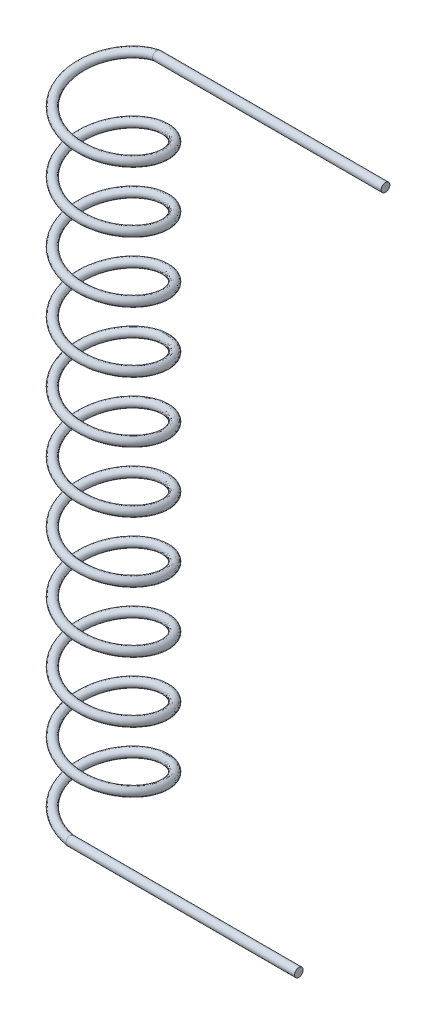
SolidWorks part; units mm, degrees
ref_plane "Front Plane" through (0, 0, 0) normal (0, 0, 1) x (1, 0, 0)
ref_plane "Top Plane" through (0, 0, 0) normal (0, 1, 0) x (1, 0, 0)
ref_plane "Right Plane" through (0, 0, 0) normal (1, 0, 0) x (0, 0, -1)
sketch "Sketch4" plane through (0, 0, 0) normal (0, 1, 0) x (1, 0, 0)
  circle A0 centre (0, 0) radius 25
  dimension "D1" = 50
curve "Helix/Spiral1" pitch 35 height 367.5 turns 10.5
sketch "Sketch5" plane through (0, 0, 0) normal (1, 0, 0) x (0, 0, -1)
  circle A0 centre (-25, 0) radius 2.5
  spline S0 degree 3 poles (-25, 0) (-25, 0.5196) (-24.3389, 1.5646) (-21.4416, 3.1275) (-16.8654, 4.6915) (-10.9687, 6.2553) (-4.2132, 7.8192) (2.8722, 9.383) (9.7327, 10.9468) (15.8311, 12.5106) (20.6901, 14.0745) (23.929, 15.6383) (25.2943, 17.2021) (24.6792, 18.766) (22.1318, 20.3298) (17.8514, 21.8936) (12.1734, 23.4574) (5.5422, 25.0213) (-1.5229, 26.5851) (-8.4688, 28.1489) (-14.7516, 29.7128) (-19.8794, 31.2766) (-23.4507, 32.8404) (-25.1858, 34.4043) (-24.949, 35.9681) (-22.7587, 37.5319) (-18.7865, 39.0957) (-13.3433, 40.6596) (-6.8554, 42.2234) (0.1693, 43.7872) (7.1807, 45.3511) (13.6299, 46.9149) (19.0119, 48.4787) (22.9053, 50.0426) (25.0053, 51.6064) (25.1474, 53.1702) (23.3206, 54.734) (19.6678, 56.2979) (14.475, 57.8617) (8.1489, 59.4255) (1.1848, 60.9894) (-5.8721, 62.5532) (-12.4693, 64.117) (-18.0901, 65.6809) (-22.2945, 67.2447) (-24.7533, 68.8085) (-25.274, 70.3723) (-23.8158, 71.9362) (-20.4928, 73.5) (-15.5654, 75.0638) (-9.4192, 76.6277) (-2.5355, 78.1915) (4.5467, 79.7553) (11.273, 81.3191) (17.1165, 82.883) (21.6199, 84.4468) (24.4305, 86.0106) (25.3283, 87.5745) (24.2429, 89.1383) (21.2593, 90.7021) (16.6112, 92.266) (10.6625, 93.8298) (3.8789, 95.3936) (-3.2084, 96.9574) (-10.0444, 98.5213) (-16.0941, 100.0851) (-20.8836, 101.6489) (-24.0379, 103.2128) (-25.3102, 104.7766) (-24.6007, 106.3404) (-21.9651, 107.9043) (-17.6096, 109.4681) (-11.8754, 111.0319) (-5.2113, 112.5957) (1.8608, 114.1596) (8.7872, 115.7234) (15.0256, 117.2872) (20.0875, 118.8511) (23.5766, 120.4149) (25.2197, 121.9787) (24.8882, 123.5426) (22.608, 125.1064) (18.5576, 126.6702) (13.0543, 128.234) (6.5288, 129.7979) (-0.5079, 131.3617) (-7.5048, 132.9255) (-13.9141, 134.4894) (-19.234, 136.0532) (-23.0479, 137.617) (-25.0572, 139.1809) (-25.1045, 140.7447) (-23.1863, 142.3085) (-19.4526, 143.8723) (-14.1958, 145.4362) (-7.8276, 147) (-0.8464, 148.5638) (6.201, 150.1277) (12.7629, 151.6915) (18.3255, 153.2553) (22.4533, 154.8191) (24.823, 156.383) (25.2491, 157.9468) (23.6983, 159.5106) (20.292, 161.0745) (15.2968, 162.6383) (9.104, 164.2021) (2.1983, 165.766) (-4.8795, 167.3298) (-11.5752, 168.8936) (-17.3646, 170.4574) (-21.7944, 172.0213) (-24.5178, 173.5851) (-25.3215, 175.1489) (-24.1426, 176.7128) (-21.0733, 178.2766) (-16.3541, 179.8404) (-10.3544, 181.4043) (-3.544, 182.9681) (3.544, 184.5319) (10.3544, 186.0957) (16.3541, 187.6596) (21.0733, 189.2234) (24.1426, 190.7872) (25.3215, 192.3511) (24.5178, 193.9149) (21.7944, 195.4787) (17.3646, 197.0426) (11.5752, 198.6064) (4.8795, 200.1702) (-2.1983, 201.734) (-9.104, 203.2979) (-15.2968, 204.8617) (-20.292, 206.4255) (-23.6983, 207.9894) (-25.2491, 209.5532) (-24.823, 211.117) (-22.4533, 212.6809) (-18.3255, 214.2447) (-12.7629, 215.8085) (-6.201, 217.3723) (0.8464, 218.9362) (7.8276, 220.5) (14.1958, 222.0638) (19.4526, 223.6277) (23.1863, 225.1915) (25.1045, 226.7553) (25.0572, 228.3191) (23.0479, 229.883) (19.234, 231.4468) (13.9141, 233.0106) (7.5048, 234.5745) (0.5079, 236.1383) (-6.5288, 237.7021) (-13.0543, 239.266) (-18.5576, 240.8298) (-22.608, 242.3936) (-24.8882, 243.9574) (-25.2197, 245.5213) (-23.5766, 247.0851) (-20.0875, 248.6489) (-15.0256, 250.2128) (-8.7872, 251.7766) (-1.8608, 253.3404) (5.2113, 254.9043) (11.8754, 256.4681) (17.6096, 258.0319) (21.9651, 259.5957) (24.6007, 261.1596) (25.3102, 262.7234) (24.0379, 264.2872) (20.8836, 265.8511) (16.0941, 267.4149) (10.0444, 268.9787) (3.2084, 270.5426) (-3.8789, 272.1064) (-10.6625, 273.6702) (-16.6112, 275.234) (-21.2593, 276.7979) (-24.2429, 278.3617) (-25.3283, 279.9255) (-24.4305, 281.4894) (-21.6199, 283.0532) (-17.1165, 284.617) (-11.273, 286.1809) (-4.5467, 287.7447) (2.5355, 289.3085) (9.4192, 290.8723) (15.5654, 292.4362) (20.4928, 294) (23.8158, 295.5638) (25.274, 297.1277) (24.7533, 298.6915) (22.2945, 300.2553) (18.0901, 301.8191) (12.4693, 303.383) (5.8721, 304.9468) (-1.1848, 306.5106) (-8.1489, 308.0745) (-14.475, 309.6383) (-19.6678, 311.2021) (-23.3206, 312.766) (-25.1474, 314.3298) (-25.0053, 315.8936) (-22.9053, 317.4574) (-19.0119, 319.0213) (-13.6299, 320.5851) (-7.1807, 322.1489) (-0.1693, 323.7128) (6.8554, 325.2766) (13.3433, 326.8404) (18.7865, 328.4043) (22.7587, 329.9681) (24.949, 331.5319) (25.1858, 333.0957) (23.4507, 334.6596) (19.8794, 336.2234) (14.7516, 337.7872) (8.4688, 339.3511) (1.5229, 340.9149) (-5.5422, 342.4787) (-12.1734, 344.0426) (-17.8514, 345.6064) (-22.1318, 347.1702) (-24.6792, 348.734) (-25.2943, 350.2979) (-23.929, 351.8617) (-20.6901, 353.4255) (-15.8311, 354.9894) (-9.7327, 356.5532) (-2.8722, 358.117) (4.2132, 359.6808) (10.9687, 361.2447) (16.8654, 362.8085) (21.4416, 364.3725) (24.3389, 365.9354) (25, 366.9804) (25, 367.5) knots 0 0 0 0 0.004255 0.008511 0.012766 0.017021 0.021277 0.025532 0.029787 0.034043 0.038298 0.042553 0.046809 0.051064 0.055319 0.059574 0.06383 0.068085 0.07234 0.076596 0.080851 0.085106 0.089362 0.093617 0.097872 0.102128 0.106383 0.110638 0.114894 0.119149 0.123404 0.12766 0.131915 0.13617 0.140426 0.144681 0.148936 0.153191 0.157447 0.161702 0.165957 0.170213 0.174468 0.178723 0.182979 0.187234 0.191489 0.195745 0.2 0.204255 0.208511 0.212766 0.217021 0.221277 0.225532 0.229787 0.234043 0.238298 0.242553 0.246809 0.251064 0.255319 0.259574 0.26383 0.268085 0.27234 0.276596 0.280851 0.285106 0.289362 0.293617 0.297872 0.302128 0.306383 0.310638 0.314894 0.319149 0.323404 0.32766 0.331915 0.33617 0.340426 0.344681 0.348936 0.353191 0.357447 0.361702 0.365957 0.370213 0.374468 0.378723 0.382979 0.387234 0.391489 0.395745 0.4 0.404255 0.408511 0.412766 0.417021 0.421277 0.425532 0.429787 0.434043 0.438298 0.442553 0.446809 0.451064 0.455319 0.459574 0.46383 0.468085 0.47234 0.476596 0.480851 0.485106 0.489362 0.493617 0.497872 0.502128 0.506383 0.510638 0.514894 0.519149 0.523404 0.52766 0.531915 0.53617 0.540426 0.544681 0.548936 0.553191 0.557447 0.561702 0.565957 0.570213 0.574468 0.578723 0.582979 0.587234 0.591489 0.595745 0.6 0.604255 0.608511 0.612766 0.617021 0.621277 0.625532 0.629787 0.634043 0.638298 0.642553 0.646809 0.651064 0.655319 0.659574 0.66383 0.668085 0.67234 0.676596 0.680851 0.685106 0.689362 0.693617 0.697872 0.702128 0.706383 0.710638 0.714894 0.719149 0.723404 0.72766 0.731915 0.73617 0.740426 0.744681 0.748936 0.753191 0.757447 0.761702 0.765957 0.770213 0.774468 0.778723 0.782979 0.787234 0.791489 0.795745 0.8 0.804255 0.808511 0.812766 0.817021 0.821277 0.825532 0.829787 0.834043 0.838298 0.842553 0.846809 0.851064 0.855319 0.859574 0.86383 0.868085 0.87234 0.876596 0.880851 0.885106 0.889362 0.893617 0.897872 0.902128 0.906383 0.910638 0.914894 0.919149 0.923404 0.92766 0.931915 0.93617 0.940426 0.944681 0.948936 0.953191 0.957447 0.961702 0.965957 0.970213 0.974468 0.978723 0.982979 0.987234 0.991489 0.995745 1 1 1 1 construction
  dimension "D1" = 5
sweep "Sweep1" add profiles "Sketch5" path "Helix/Spiral1"
sketch "Sketch6" plane through (0, 0, 0) normal (1, 0, 0) x (0, 0, -1)
  circle A0 centre (25, 367.5) radius 2.5
  circle A1 centre (-25, 0) radius 2.5
  spline S0 degree 3 poles (-25, 0) (-25, 0.5196) (-24.3389, 1.5646) (-21.4416, 3.1275) (-16.8654, 4.6915) (-10.9687, 6.2553) (-4.2132, 7.8192) (2.8722, 9.383) (9.7327, 10.9468) (15.8311, 12.5106) (20.6901, 14.0745) (23.929, 15.6383) (25.2943, 17.2021) (24.6792, 18.766) (22.1318, 20.3298) (17.8514, 21.8936) (12.1734, 23.4574) (5.5422, 25.0213) (-1.5229, 26.5851) (-8.4688, 28.1489) (-14.7516, 29.7128) (-19.8794, 31.2766) (-23.4507, 32.8404) (-25.1858, 34.4043) (-24.949, 35.9681) (-22.7587, 37.5319) (-18.7865, 39.0957) (-13.3433, 40.6596) (-6.8554, 42.2234) (0.1693, 43.7872) (7.1807, 45.3511) (13.6299, 46.9149) (19.0119, 48.4787) (22.9053, 50.0426) (25.0053, 51.6064) (25.1474, 53.1702) (23.3206, 54.734) (19.6678, 56.2979) (14.475, 57.8617) (8.1489, 59.4255) (1.1848, 60.9894) (-5.8721, 62.5532) (-12.4693, 64.117) (-18.0901, 65.6809) (-22.2945, 67.2447) (-24.7533, 68.8085) (-25.274, 70.3723) (-23.8158, 71.9362) (-20.4928, 73.5) (-15.5654, 75.0638) (-9.4192, 76.6277) (-2.5355, 78.1915) (4.5467, 79.7553) (11.273, 81.3191) (17.1165, 82.883) (21.6199, 84.4468) (24.4305, 86.0106) (25.3283, 87.5745) (24.2429, 89.1383) (21.2593, 90.7021) (16.6112, 92.266) (10.6625, 93.8298) (3.8789, 95.3936) (-3.2084, 96.9574) (-10.0444, 98.5213) (-16.0941, 100.0851) (-20.8836, 101.6489) (-24.0379, 103.2128) (-25.3102, 104.7766) (-24.6007, 106.3404) (-21.9651, 107.9043) (-17.6096, 109.4681) (-11.8754, 111.0319) (-5.2113, 112.5957) (1.8608, 114.1596) (8.7872, 115.7234) (15.0256, 117.2872) (20.0875, 118.8511) (23.5766, 120.4149) (25.2197, 121.9787) (24.8882, 123.5426) (22.608, 125.1064) (18.5576, 126.6702) (13.0543, 128.234) (6.5288, 129.7979) (-0.5079, 131.3617) (-7.5048, 132.9255) (-13.9141, 134.4894) (-19.234, 136.0532) (-23.0479, 137.617) (-25.0572, 139.1809) (-25.1045, 140.7447) (-23.1863, 142.3085) (-19.4526, 143.8723) (-14.1958, 145.4362) (-7.8276, 147) (-0.8464, 148.5638) (6.201, 150.1277) (12.7629, 151.6915) (18.3255, 153.2553) (22.4533, 154.8191) (24.823, 156.383) (25.2491, 157.9468) (23.6983, 159.5106) (20.292, 161.0745) (15.2968, 162.6383) (9.104, 164.2021) (2.1983, 165.766) (-4.8795, 167.3298) (-11.5752, 168.8936) (-17.3646, 170.4574) (-21.7944, 172.0213) (-24.5178, 173.5851) (-25.3215, 175.1489) (-24.1426, 176.7128) (-21.0733, 178.2766) (-16.3541, 179.8404) (-10.3544, 181.4043) (-3.544, 182.9681) (3.544, 184.5319) (10.3544, 186.0957) (16.3541, 187.6596) (21.0733, 189.2234) (24.1426, 190.7872) (25.3215, 192.3511) (24.5178, 193.9149) (21.7944, 195.4787) (17.3646, 197.0426) (11.5752, 198.6064) (4.8795, 200.1702) (-2.1983, 201.734) (-9.104, 203.2979) (-15.2968, 204.8617) (-20.292, 206.4255) (-23.6983, 207.9894) (-25.2491, 209.5532) (-24.823, 211.117) (-22.4533, 212.6809) (-18.3255, 214.2447) (-12.7629, 215.8085) (-6.201, 217.3723) (0.8464, 218.9362) (7.8276, 220.5) (14.1958, 222.0638) (19.4526, 223.6277) (23.1863, 225.1915) (25.1045, 226.7553) (25.0572, 228.3191) (23.0479, 229.883) (19.234, 231.4468) (13.9141, 233.0106) (7.5048, 234.5745) (0.5079, 236.1383) (-6.5288, 237.7021) (-13.0543, 239.266) (-18.5576, 240.8298) (-22.608, 242.3936) (-24.8882, 243.9574) (-25.2197, 245.5213) (-23.5766, 247.0851) (-20.0875, 248.6489) (-15.0256, 250.2128) (-8.7872, 251.7766) (-1.8608, 253.3404) (5.2113, 254.9043) (11.8754, 256.4681) (17.6096, 258.0319) (21.9651, 259.5957) (24.6007, 261.1596) (25.3102, 262.7234) (24.0379, 264.2872) (20.8836, 265.8511) (16.0941, 267.4149) (10.0444, 268.9787) (3.2084, 270.5426) (-3.8789, 272.1064) (-10.6625, 273.6702) (-16.6112, 275.234) (-21.2593, 276.7979) (-24.2429, 278.3617) (-25.3283, 279.9255) (-24.4305, 281.4894) (-21.6199, 283.0532) (-17.1165, 284.617) (-11.273, 286.1809) (-4.5467, 287.7447) (2.5355, 289.3085) (9.4192, 290.8723) (15.5654, 292.4362) (20.4928, 294) (23.8158, 295.5638) (25.274, 297.1277) (24.7533, 298.6915) (22.2945, 300.2553) (18.0901, 301.8191) (12.4693, 303.383) (5.8721, 304.9468) (-1.1848, 306.5106) (-8.1489, 308.0745) (-14.475, 309.6383) (-19.6678, 311.2021) (-23.3206, 312.766) (-25.1474, 314.3298) (-25.0053, 315.8936) (-22.9053, 317.4574) (-19.0119, 319.0213) (-13.6299, 320.5851) (-7.1807, 322.1489) (-0.1693, 323.7128) (6.8554, 325.2766) (13.3433, 326.8404) (18.7865, 328.4043) (22.7587, 329.9681) (24.949, 331.5319) (25.1858, 333.0957) (23.4507, 334.6596) (19.8794, 336.2234) (14.7516, 337.7872) (8.4688, 339.3511) (1.5229, 340.9149) (-5.5422, 342.4787) (-12.1734, 344.0426) (-17.8514, 345.6064) (-22.1318, 347.1702) (-24.6792, 348.734) (-25.2943, 350.2979) (-23.929, 351.8617) (-20.6901, 353.4255) (-15.8311, 354.9894) (-9.7327, 356.5532) (-2.8722, 358.117) (4.2132, 359.6808) (10.9687, 361.2447) (16.8654, 362.8085) (21.4416, 364.3725) (24.3389, 365.9354) (25, 366.9804) (25, 367.5) knots 0 0 0 0 0.004255 0.008511 0.012766 0.017021 0.021277 0.025532 0.029787 0.034043 0.038298 0.042553 0.046809 0.051064 0.055319 0.059574 0.06383 0.068085 0.07234 0.076596 0.080851 0.085106 0.089362 0.093617 0.097872 0.102128 0.106383 0.110638 0.114894 0.119149 0.123404 0.12766 0.131915 0.13617 0.140426 0.144681 0.148936 0.153191 0.157447 0.161702 0.165957 0.170213 0.174468 0.178723 0.182979 0.187234 0.191489 0.195745 0.2 0.204255 0.208511 0.212766 0.217021 0.221277 0.225532 0.229787 0.234043 0.238298 0.242553 0.246809 0.251064 0.255319 0.259574 0.26383 0.268085 0.27234 0.276596 0.280851 0.285106 0.289362 0.293617 0.297872 0.302128 0.306383 0.310638 0.314894 0.319149 0.323404 0.32766 0.331915 0.33617 0.340426 0.344681 0.348936 0.353191 0.357447 0.361702 0.365957 0.370213 0.374468 0.378723 0.382979 0.387234 0.391489 0.395745 0.4 0.404255 0.408511 0.412766 0.417021 0.421277 0.425532 0.429787 0.434043 0.438298 0.442553 0.446809 0.451064 0.455319 0.459574 0.46383 0.468085 0.47234 0.476596 0.480851 0.485106 0.489362 0.493617 0.497872 0.502128 0.506383 0.510638 0.514894 0.519149 0.523404 0.52766 0.531915 0.53617 0.540426 0.544681 0.548936 0.553191 0.557447 0.561702 0.565957 0.570213 0.574468 0.578723 0.582979 0.587234 0.591489 0.595745 0.6 0.604255 0.608511 0.612766 0.617021 0.621277 0.625532 0.629787 0.634043 0.638298 0.642553 0.646809 0.651064 0.655319 0.659574 0.66383 0.668085 0.67234 0.676596 0.680851 0.685106 0.689362 0.693617 0.697872 0.702128 0.706383 0.710638 0.714894 0.719149 0.723404 0.72766 0.731915 0.73617 0.740426 0.744681 0.748936 0.753191 0.757447 0.761702 0.765957 0.770213 0.774468 0.778723 0.782979 0.787234 0.791489 0.795745 0.8 0.804255 0.808511 0.812766 0.817021 0.821277 0.825532 0.829787 0.834043 0.838298 0.842553 0.846809 0.851064 0.855319 0.859574 0.86383 0.868085 0.87234 0.876596 0.880851 0.885106 0.889362 0.893617 0.897872 0.902128 0.906383 0.910638 0.914894 0.919149 0.923404 0.92766 0.931915 0.93617 0.940426 0.944681 0.948936 0.953191 0.957447 0.961702 0.965957 0.970213 0.974468 0.978723 0.982979 0.987234 0.991489 0.995745 1 1 1 1 construction
  dimension "D1" = 5
  dimension "D2" = 5
extrude "Boss-Extrude1" add sketch "Sketch6" along normal blind 132
sketch "Sketch7" plane through (0, 0, 0) normal (1, 0, 0) x (0, 0, -1)
  line L0 (0, 0) -> (0, 393.6957) construction
